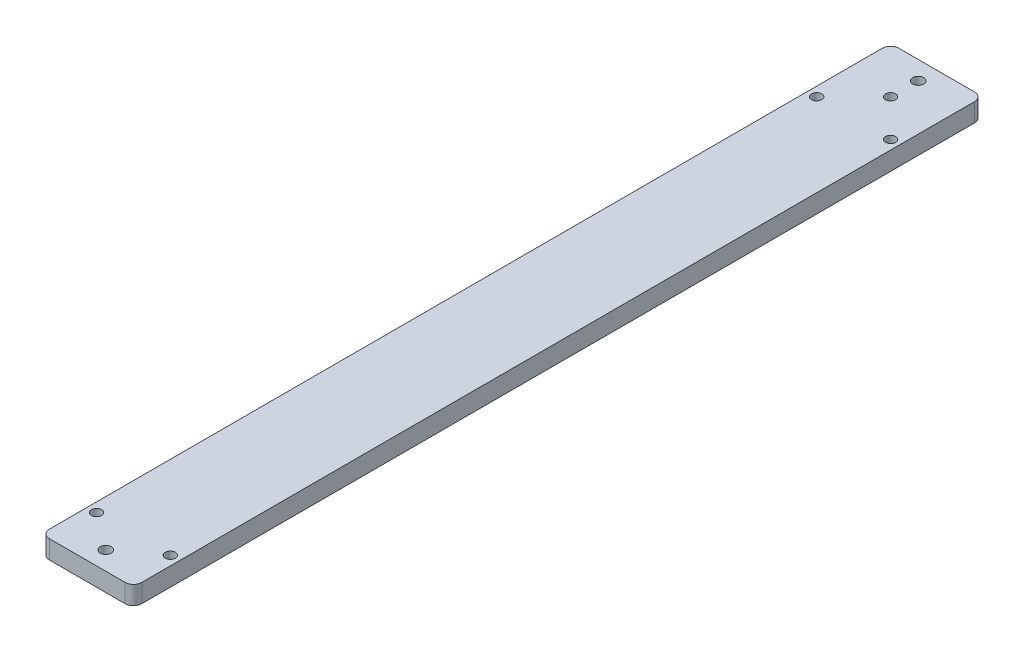
SolidWorks part; units mm, degrees
ref_plane "Front Plane" through (0, 0, 0) normal (0, 0, 1) x (1, 0, 0)
ref_plane "Top Plane" through (0, 0, 0) normal (0, 1, 0) x (1, 0, 0)
ref_plane "Right Plane" through (0, 0, 0) normal (1, 0, 0) x (0, 0, -1)
sketch "Sketch1" plane through (0, 0, 0) normal (0, -1, 0) x (1, 0, 0)
  line L1 (37.3533, 24.6922) -> (-12.6467, 24.6922)
  line L2 (37.3533, 24.6922) -> (37.3533, 484.6922)
  line L3 (37.3533, 484.6922) -> (-12.6467, 484.6922)
  line L4 (-12.6467, 24.6922) -> (-12.6467, 484.6922)
  dimension "D1" = 460
  dimension "D2" = 50
extrude "Boss-Extrude1" add sketch "Sketch1" along normal blind 10
sketch "Sketch2" plane through (0, -10, 0) normal (0, -1, 0) x (1, 0, 0)
  circle A0 centre (32.3533, 69.6922) radius 2.75
  circle A1 centre (-7.6467, 69.6922) radius 2.75
  circle A2 centre (12.3533, 49.6922) radius 2.75
  dimension "D1" = 5.5
  dimension "D2" = 5.5
  dimension "D3" = 5.5
extrude "Cut-Extrude1" cut sketch "Sketch2" against normal up to next
sketch "Sketch3" plane through (0, -10, 0) normal (0, -1, 0) x (1, 0, 0)
  circle A0 centre (-7.6467, 69.6922) radius 4.5
  circle A1 centre (32.3533, 69.6922) radius 4.5
  circle A2 centre (12.3533, 49.6922) radius 4.5
  dimension "D1" = 9
  dimension "D2" = 9
  dimension "D3" = 9
extrude "Cut-Extrude2" cut sketch "Sketch3" against normal blind 5.5
sketch "Sketch4" plane through (0, -10, 0) normal (0, -1, 0) x (1, 0, 0)
  circle A0 centre (-7.6467, 459.6922) radius 2.75
  circle A1 centre (32.3533, 459.6922) radius 2.75
  dimension "D1" = 5.5
  dimension "D2" = 5.5
extrude "Cut-Extrude3" cut sketch "Sketch4" against normal up to next
sketch "Sketch5" plane through (0, -10, 0) normal (0, -1, 0) x (1, 0, 0)
  circle A0 centre (-7.6467, 459.6922) radius 4.5
  circle A1 centre (32.3533, 459.6922) radius 4.5
  dimension "D1" = 9
  dimension "D2" = 9
extrude "Cut-Extrude4" cut sketch "Sketch5" against normal blind 5.5
fillet "Fillet2" radius 4.5 4 edges at (37.3533, -5, 24.6922) (-12.6467, -5, 24.6922) (37.3533, -5, 484.6922) (-12.6467, -5, 484.6922)
sketch "Sketch6" plane through (0, 0, 0) normal (0, 1, 0) x (-1, 0, 0)
  line L0 (8.1467, 24.6922) -> (-32.8533, 24.6922) construction
  line L1 (-37.3533, 29.1922) -> (-37.3533, 480.1922) construction
  line L2 (-32.8533, 484.6922) -> (8.1467, 484.6922) construction
  circle A0 centre (-12.3533, 474.6922) radius 3
  circle A1 centre (-12.3533, 34.6922) radius 3
  dimension "D2" = 6
  dimension "D6" = 6
  dimension "D1" = 10
  dimension "D3" = 25
  dimension "D4" = 10
  dimension "D5" = 25
extrude "Cut-Extrude5" cut sketch "Sketch6" against normal up to next
